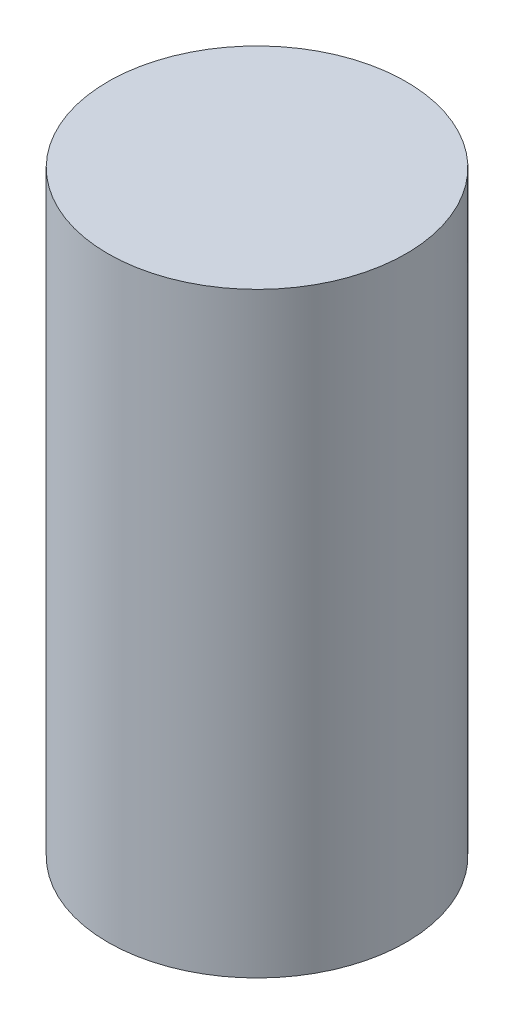
SolidWorks part; units mm, degrees
ref_plane "Front Plane" through (0, 0, 0) normal (0, 0, 1) x (1, 0, 0)
ref_plane "Top Plane" through (0, 0, 0) normal (0, 1, 0) x (1, 0, 0)
ref_plane "Right Plane" through (0, 0, 0) normal (1, 0, 0) x (0, 0, -1)
sketch "Sketch1" plane through (0, 0, 0) normal (0, 1, 0) x (1, 0, 0)
  circle A0 centre (0, 0) radius 5
  dimension "D1" = 10
extrude "Boss-Extrude1" add sketch "Sketch1" along normal mid plane 20
